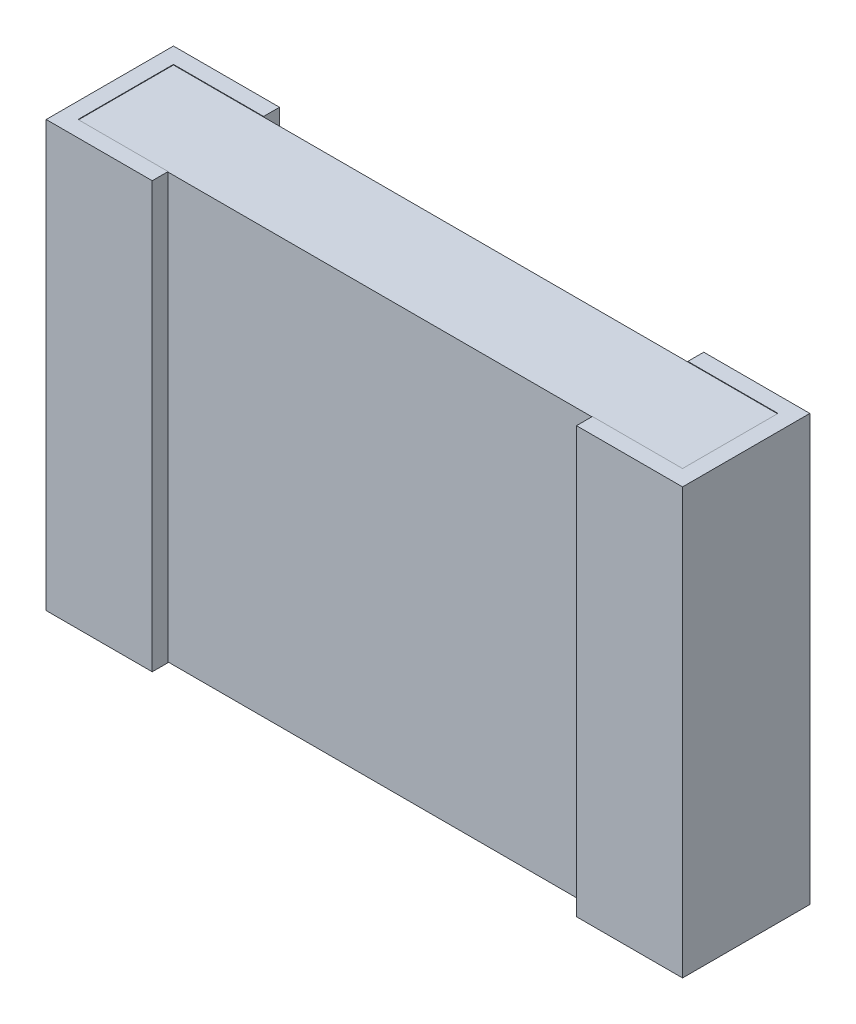
SolidWorks part; units mm, degrees
ref_plane "x/y" through (0, 0, 0) normal (0, 0, 1) x (1, 0, 0)
ref_plane "x/z" through (0, 0, 0) normal (0, 1, 0) x (1, 0, 0)
ref_plane "y/z" through (0, 0, 0) normal (1, 0, 0) x (0, 0, -1)
sketch "Sketch2" plane through (0, 0, 0) normal (0, 1, 0) x (1, 0, 0)
  line L0 (0.0762, -0.5334) -> (2.9718, -0.5334)
  line L1 (0.0762, -0.5334) -> (0.0762, -0.0762)
  line L2 (2.9718, -0.0762) -> (0.0762, -0.0762)
  line L3 (2.9718, -0.0762) -> (2.9718, -0.5334)
  dimension "D1" = 2.8956
  dimension "D2" = 0.4572
  dimension "D3" = 0.0762
extrude "Base-Extrude" add sketch "Sketch2" along normal mid plane 2.032
ref_plane "Plane4" through (0, 1.0185, 0) normal (0, 1, 0) x (-1, 0, 0)
sketch "Sketch3" plane through (0, 1.0185, 0) normal (0, 1, 0) x (-1, 0, 0)
  line L0 (-0.508, 0.6096) -> (-0.508, 0.5334)
  line L1 (-0.0762, 0.5334) -> (-2.9718, 0.5334) construction
  line L2 (-0.508, 0) -> (0, 0)
  line L3 (0, 0) -> (0, 0.6096)
  line L4 (0, 0.6096) -> (-0.508, 0.6096)
  line L5 (-0.508, 0.0762) -> (-0.508, 0)
  line L6 (-0.508, 0.0762) -> (-0.0762, 0.0762)
  line L7 (-0.0762, 0.0762) -> (-0.0762, 0.5334)
  line L8 (-0.0762, 0.5334) -> (-0.508, 0.5334)
  dimension "D1" = 0.508
  dimension "D2" = 0.508
extrude "Boss-Extrude8" add sketch "Sketch3" against normal blind 2.0371
ref_plane "Plane6" through (1.524, 0, 0) normal (1, 0, 0) x (0, 0, -1)
mirror "Mirror5" about plane through (1.524, 0, 0) normal (1, 0, 0) of "Boss-Extrude8"
